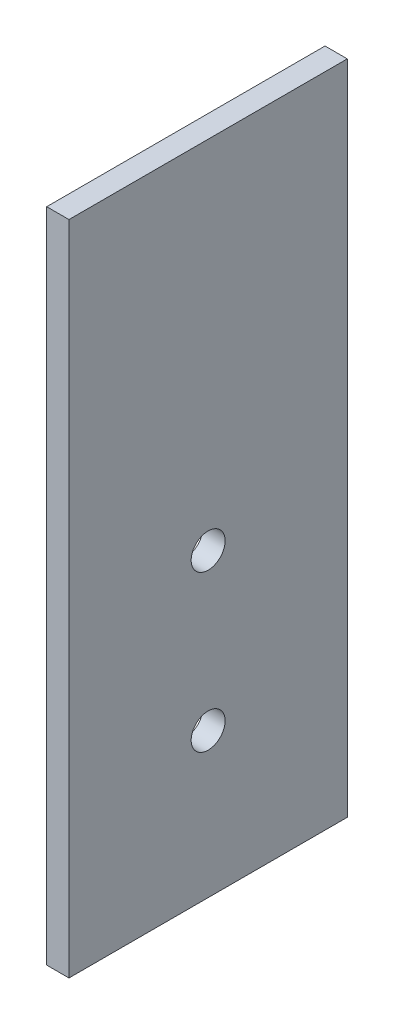
SolidWorks part; units mm, degrees
ref_plane "Front Plane" through (0, 0, 0) normal (0, 0, 1) x (1, 0, 0)
ref_plane "Top Plane" through (0, 0, 0) normal (0, 1, 0) x (1, 0, 0)
ref_plane "Right Plane" through (0, 0, 0) normal (1, 0, 0) x (0, 0, -1)
sketch "Sketch1" plane through (0, 0, 0) normal (1, 0, 0) x (0, 0, -1)
  line L1 (-25, 42.1044) -> (0, 42.1044)
  line L2 (-25, 42.1044) -> (-25, -16.8956)
  line L3 (-25, -16.8956) -> (0, -16.8956)
  line L4 (0, 42.1044) -> (0, -16.8956)
  dimension "D1" = 59
  dimension "D2" = 25
extrude "Boss-Extrude1" add sketch "Sketch1" along normal blind 2
sketch "Sketch3" plane through (0, 0, 0) normal (-1, 0, 0) x (0, 0, 1)
  line L0 (25, -16.8956) -> (0, -16.8956) construction
  line L1 (25, 42.1044) -> (25, -16.8956) construction
  circle A0 centre (12.5, -3.8956) radius 1.525
  circle A1 centre (12.5, 10.1044) radius 1.525
  dimension "D1" = 3.05
  dimension "D2" = 3.05
  dimension "D3" = 13
  dimension "D4" = 14
  dimension "D5" = 12.5
extrude "Cut-Extrude1" cut sketch "Sketch3" against normal through all
